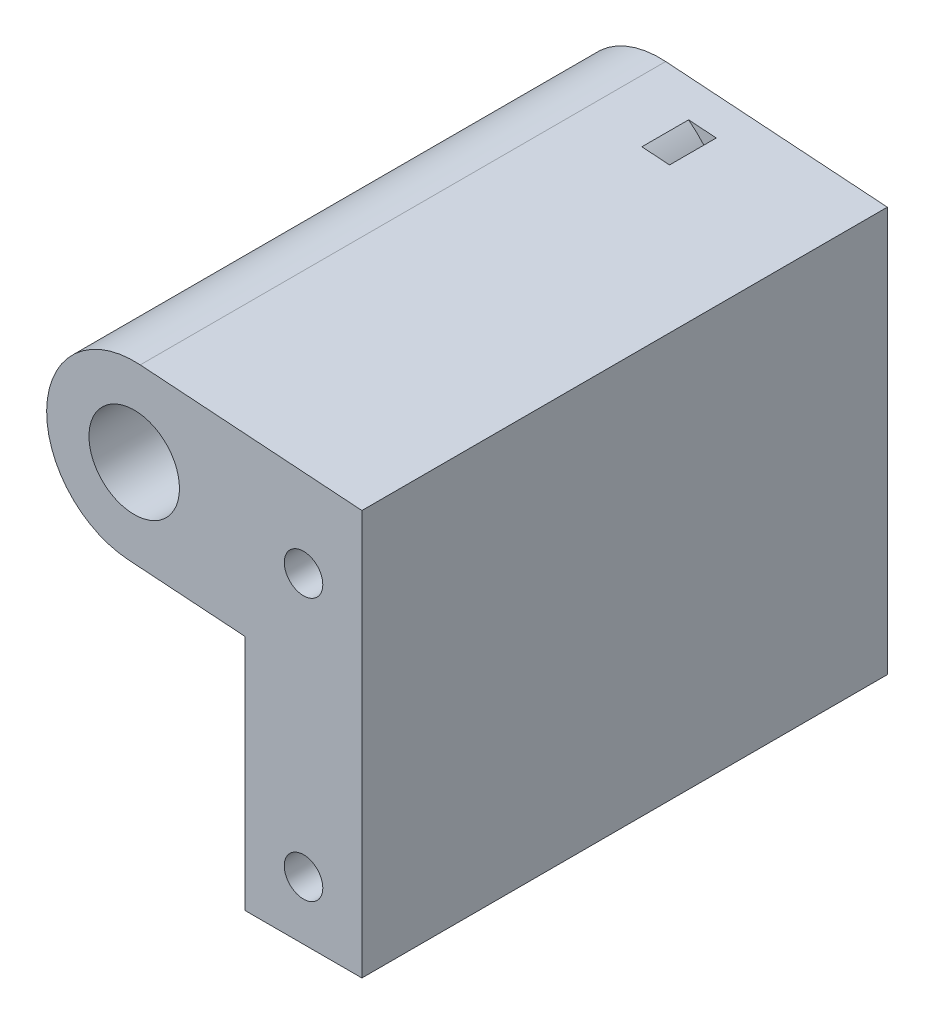
SolidWorks part; units mm, degrees
ref_plane "Front Plane" through (0, 0, 0) normal (0, 0, 1) x (1, 0, 0)
ref_plane "Top Plane" through (0, 0, 0) normal (0, 1, 0) x (1, 0, 0)
ref_plane "Right Plane" through (0, 0, 0) normal (1, 0, 0) x (0, 0, -1)
sketch "Sketch1" plane through (0, 0, 0) normal (0, 0, 1) x (1, 0, 0)
  line L0 (-182, 170) -> (-167.5, 169) construction
  line L1 (-167.5, 169) -> (-167.5, 146.5) construction
  line L2 (-182.516, 162.5178) -> (-172.5, 161.827)
  line L3 (-172.5, 161.827) -> (-172.5, 141.5)
  line L4 (-181.484, 177.4822) -> (-162.5, 176.173)
  line L5 (-162.5, 176.173) -> (-162.5, 141.5)
  line L6 (-172.5, 141.5) -> (-162.5, 141.5)
  line L7 (-167.5, 146.5) -> (-167.5, 141.5) construction
  circle A0 centre (-167.5, 146.5) radius 2.4 construction
  circle A3 centre (-167.5, 146.5) radius 2.4 construction
  circle A4 centre (-167.5, 169) radius 2.4 construction
  arc A5 (-182.516, 162.5178) -> (-181.484, 177.4822) centre (-182, 170) ccw
  dimension "D1" = 7.5
  dimension "D6" = 4.8
  dimension "D3" = 5
  dimension "D4" = 14.5
  dimension "D5" = 23.5
  dimension "D2" = 22.5
  dimension "D7" = 5
  dimension "D8" = 7.5
  dimension "D9" = 5
extrude "Boss-Extrude1" add sketch "Sketch1" along normal blind 45 contours L5 L6 L3 L2 A5 L4
sketch "Sketch2" plane through (0, 0, 0) normal (0, 0, -1) x (-1, 0, 0)
  line L0 (162.5, 176.173) -> (181.484, 177.4822) construction
  line L2 (182.516, 162.5178) -> (172.5, 161.827) construction
  arc A0 (176.5208, 177.1399) -> (177.5529, 162.1755) centre (182, 170) ccw
  arc A1 (181.484, 177.4822) -> (182.516, 162.5178) centre (182, 170) ccw construction
  arc A3 (175.6076, 178.3299) -> (176.8117, 160.8714) centre (182, 170) ccw
  arc A4 (176.5208, 177.1399) -> (175.6076, 178.3299) centre (176.0642, 177.7349) ccw
  arc A5 (177.5529, 162.1755) -> (176.8117, 160.8714) centre (177.1823, 161.5234) cw
  point P8 (177.508, 162.1724)
  point P9 (0, 0)
  point P10 (0, 0)
  point P11 (182.1468, 160.2513)
  point P17 (0, 0)
  dimension "D1" = 9
  dimension "D2" = 1.5
extrude "Cut-Extrude1" cut sketch "Sketch2" against normal mid plane 4 from offset 5 offset against normal yes
ref_plane "Plane1" through (0, 0, 22.5) normal (0, 0, -1) x (-1, 0, 0)
mirror "Mirror1" [suppressed] about plane through (0, 0, 22.5) normal (0, 0, -1)
hole_wizard "M4x0.7 Tapped Hole1" positions "Sketch3" profile "Sketch4" tap size "M4x0.7" standard "ANSI Metric" end condition through all
sketch "Sketch3" plane through (0, 0, 45) normal (0, 0, 1) x (1, 0, 0)
  point P0 (-167.5, 169)
  point P3 (-167.5, 146.5)
sketch "Sketch4" plane through (-167.5, 169, 45) normal (1, 0, 0) x (0, -1, 0)
  line L0 (0, 0) -> (0, 45)
  line L1 (0, 45) -> (1.65, 45)
  line L2 (1.65, 45) -> (1.65, 0)
  line L5 (1.65, 0) -> (0, 0)
  line L11 (0, -6.35) -> (0, 107.95) construction
  dimension "Thru Tap Drill Dia." = 3.3
  dimension "Thru Tap Drill Depth" = 45
cosmetic thread "Hole Thread1" parameters "D2"=4
cosmetic thread "Hole Thread2" parameters "D2"=4
sketch "Sketch5" plane through (0, 0, 45) normal (0, 0, 1) x (1, 0, 0)
  circle A0 centre (-182, 170) radius 7.5
extrude "Boss-Extrude2" add sketch "Sketch5" against normal through all
sketch "Sketch6" plane through (0, 0, 45) normal (0, 0, 1) x (1, 0, 0)
  circle A0 centre (-182, 170) radius 3.875
  dimension "D1" = 7.75
extrude "Cut-Extrude2" cut sketch "Sketch6" against normal through all
